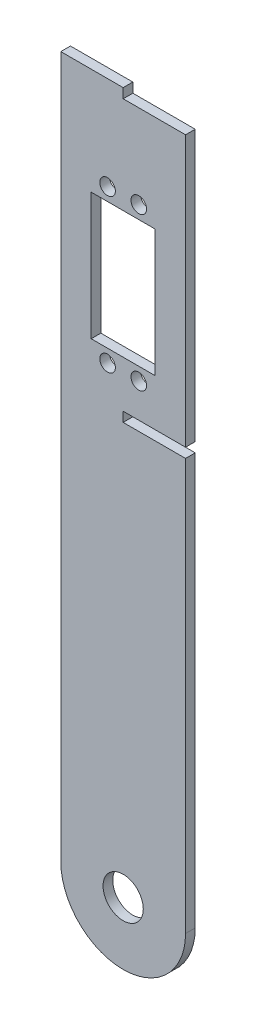
SolidWorks part; units mm, degrees
material "Teak"
ref_plane "Front Plane" through (0, 0, 0) normal (0, 0, 1) x (1, 0, 0)
ref_plane "Top Plane" through (0, 0, 0) normal (0, 1, 0) x (1, 0, 0)
ref_plane "Right Plane" through (0, 0, 0) normal (1, 0, 0) x (0, 0, -1)
sketch "Sketch1" plane through (0, 0, 0) normal (0, 0, 1) x (1, 0, 0)
  line L0 (0, 0) -> (0, 92.0821) construction
  line L1 (-1.9084, 0) -> (-100.511, 0) construction
  line L2 (-20, 0) -> (-20, 224.85)
  line L3 (-20, 224.85) -> (20, 224.85)
  line L4 (20, 0) -> (20, 224.85)
  line L5 (0, 170.35) -> (10.25, 170.35) construction
  line L6 (-10.25, 190.7) -> (10.25, 190.7)
  line L7 (-10.25, 190.7) -> (-10.25, 150)
  line L8 (-10.25, 150) -> (10.25, 150)
  line L9 (10.25, 190.7) -> (10.25, 150)
  line L10 (-10.25, 190.7) -> (10.25, 150) construction
  line L11 (-10.25, 150) -> (10.25, 190.7) construction
  arc A0 (20, 0) -> (-20, 0) centre (0, 0) cw
  circle A1 centre (0, 0) radius 6.45
  circle A2 centre (0, 160) radius 2.4407 construction
  circle A3 centre (5, 145.85) radius 2.5
  circle A4 centre (-5, 145.85) radius 2.5
  circle A5 centre (-5, 194.85) radius 2.5
  circle A6 centre (5, 194.85) radius 2.5
  point P11 (0, 170.35)
  point P12 (0, 224.85)
  point P15 (0, 246.9826)
  point P18 (0, 200)
  point P46 (0, 0)
  dimension "D1" = 40
  dimension "D6" = 5
  dimension "D7" = 10
  dimension "D9" = 49
  dimension "D11" = 224.85
  dimension "D10" = 160
  dimension "D3" = 12.9
  dimension "D2" = 30
  dimension "D4" = 40.7
  dimension "D5" = 20.5
  dimension "D8" = 10
extrude "Boss-Extrude1" add sketch "Sketch1" along normal blind 3.1
sketch "Sketch2" plane through (0, 0, 3.1) normal (0, 0, 1) x (1, 0, 0)
  line L0 (0, 224.85) -> (0, 221.75)
  line L1 (0, 224.85) -> (20.0931, 224.85)
  line L2 (0, 221.75) -> (20.0931, 221.75)
  line L3 (20.0931, 224.85) -> (20.0931, 221.75)
  line L4 (20, 224.85) -> (-20, 224.85) construction
  line L5 (0, 150) -> (0, 111.8299) construction
  line L6 (20, 135) -> (20, 131.9)
  line L7 (-10.25, 150) -> (10.25, 150) construction
  line L9 (20, 135) -> (0, 135)
  line L10 (20, 131.9) -> (0, 131.9)
  line L11 (0, 135) -> (0, 131.9)
  line L13 (20, 0) -> (20, 224.85) construction
  dimension "D2" = 3.1
  dimension "D1" = 3.1
  dimension "D3" = 15
extrude "Cut-Extrude1" cut sketch "Sketch2" against normal through all
equation "\"p\"= 20mm"
equation "\"m\"= 1"
equation "\"hole_diam\"= 4mm"
equation "\"len_grip_1\"= 50mm"
equation "\"len_grip_2\"= 50mm"
equation "\"thick\"= 3.1mm"
equation "\"thick2\"= 20mm"
equation "\"wrist_cont_bearing_diam\"=3in"
equation "\"wrist_cont_bearing_thick\"=5/16in"
equation "\"len_forearm\"= 300mm"
equation "\"wrist_bearing_diam\"=3in"
equation "\"D3@Sketch1\"=\"small_bearing_outer\"-.1"
equation "\"D1@Boss-Extrude1\"=\"thick\""
equation "\"len_link\"= 7cm"
equation "\"elbow_cont_bearing_diam\"=10cm"
equation "\"elbow_cont_bearing2_diam\"=7.5cm"
equation "\"small_bearing_outer\"=13mm"
equation "\"servo1_L\"=40.7mm"
equation "\"servo1_W\"=20.5mm"
equation "\"servo1_H\"=43.5mm"
equation "\"servo1_hL\"=49mm"
equation "\"servo1_hW\"=10mm"
equation "\"servo1_H2\"=27mm"
equation "\"D4@Sketch1\"=\"servo1_L\""
equation "\"D5@Sketch1\"=\"servo1_W\""
equation "\"D8@Sketch1\"=\"servo1_hW\""
equation "\"D9@Sketch1\"=\"servo1_hL\""
equation "\"D1@Sketch2\"=\"thick\""
equation "\"D2@Sketch2\"=\"thick\""
